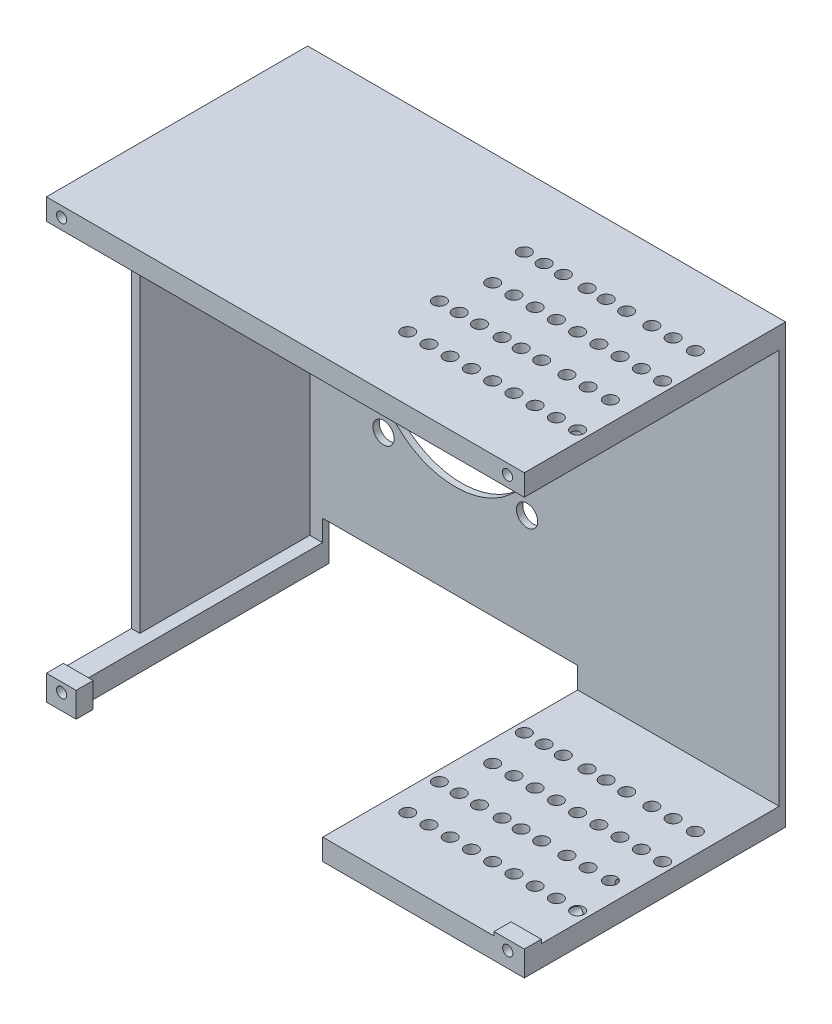
SolidWorks part; units mm, degrees
ref_plane "Front Plane" through (0, 0, 0) normal (0, 0, 1) x (1, 0, 0)
ref_plane "Top Plane" through (0, 0, 0) normal (0, 1, 0) x (1, 0, 0)
ref_plane "Right Plane" through (0, 0, 0) normal (1, 0, 0) x (0, 0, -1)
sketch "Sketch1" plane through (0, 0, 0) normal (0, 0, 1) x (1, 0, 0)
  line L1 (0, 0) -> (112.5, 0)
  line L2 (0, 0) -> (0, 103)
  line L3 (0, 103) -> (112.5, 103)
  line L4 (112.5, 0) -> (112.5, 103)
extrude "Boss-Extrude1" add sketch "Sketch1" along normal blind 1.5
sketch "Sketch2" plane through (0, 0, 1.5) normal (0, 0, 1) x (1, 0, 0)
  line L0 (112.5, 0) -> (112.5, 103) construction
  line L1 (0, 103) -> (112.5, 103)
  line L2 (0, 103) -> (0, 98)
  line L3 (0, 98) -> (112.5, 98)
  line L4 (112.5, 103) -> (112.5, 98)
extrude "Boss-Extrude2" add sketch "Sketch2" along normal blind 60
sketch "Sketch3" plane through (0, 0, 0) normal (0, 0, -1) x (-1, 0, 0)
  circle A0 centre (-36.25, 51.5) radius 19.5
  circle A1 centre (-53.1443, 68.3943) radius 2.5
  circle A2 centre (-19.3557, 68.3943) radius 2.5
  circle A3 centre (-19.3557, 34.6057) radius 2.5
  circle A4 centre (-53.1443, 34.6057) radius 2.5
  point P4 (-112.5, 103)
  point P18 (-36.25, 51.5)
  point P19 (-36.25, 51.5)
  point P25 (0, 0)
extrude "Cut-Extrude1" cut sketch "Sketch3" against normal blind 60
sketch "Sketch4" plane through (0, 0, 1.5) normal (0, 0, 1) x (1, 0, 0)
  line L0 (112.5, 0) -> (112.5, 98) construction
  line L1 (0, 0) -> (112.5, 0)
  line L2 (0, 0) -> (0, 5)
  line L3 (0, 5) -> (112.5, 5)
  line L4 (112.5, 0) -> (112.5, 5)
extrude "Boss-Extrude3" add sketch "Sketch4" along normal up to surface (60 mm away) up to face at (56.25, 100.5, 61.5)
sketch "Sketch5" plane through (0, 0, 1.5) normal (0, 0, 1) x (1, 0, 0)
  line L0 (112.5, 5) -> (0, 5) construction
  line L1 (0, 98) -> (2, 98)
  line L2 (0, 98) -> (0, 5)
  line L3 (0, 5) -> (2, 5)
  line L4 (2, 98) -> (2, 5)
extrude "Boss-Extrude4" add sketch "Sketch5" along normal blind 40
sketch "Sketch6" plane through (0, 0, 0) normal (0, 0, -1) x (-1, 0, 0)
  line L5 (0, 0) -> (-112.5, 0) construction
  line L7 (-5, 0) -> (-65.0477, 0)
  line L8 (-5, 0) -> (-5, 10)
  line L9 (-5, 10) -> (-65.0477, 10)
  line L10 (-65.0477, 0) -> (-65.0477, 10)
extrude "Cut-Extrude2" cut sketch "Sketch6" against normal blind 70
sketch "Sketch8" plane through (0, 0, 0) normal (0, -1, 0) x (1, 0, 0)
  circle A0 centre (110.0477, 46.5) radius 1.5
  circle A1 centre (105.0477, 46.5) radius 1.5
  circle A2 centre (100.0477, 46.5) radius 1.5
  circle A3 centre (95.0477, 46.5) radius 1.5
  circle A4 centre (90.0477, 46.5) radius 1.5
  circle A5 centre (85.0477, 46.5) radius 1.5
  circle A6 centre (80.0477, 46.5) radius 1.5
  circle A7 centre (75.0477, 46.5) radius 1.5
  circle A8 centre (70.0477, 46.5) radius 1.5
  circle A9 centre (107.7607, 36.5) radius 1.5
  circle A10 centre (102.5264, 36.5) radius 1.5
  circle A11 centre (97.5246, 36.5) radius 1.5
  circle A12 centre (91.5923, 36.5) radius 1.5
  circle A13 centre (86.7651, 36.5) radius 1.5
  circle A14 centre (82.2868, 36.5) radius 1.5
  circle A15 centre (76.9361, 36.5) radius 1.5
  circle A16 centre (72.167, 36.5) radius 1.5
  circle A17 centre (67.5, 36.5) radius 1.5
  circle A18 centre (110.0477, 26.5) radius 1.5
  circle A19 centre (105.0477, 26.5) radius 1.5
  circle A20 centre (100.0477, 26.5) radius 1.5
  circle A21 centre (95.0477, 26.5) radius 1.5
  circle A22 centre (90.0477, 26.5) radius 1.5
  circle A23 centre (85.0477, 26.5) radius 1.5
  circle A24 centre (80.0477, 26.5) radius 1.5
  circle A25 centre (75.0477, 26.5) radius 1.5
  circle A26 centre (70.0477, 26.5) radius 1.5
  circle A27 centre (107.7607, 16.5) radius 1.5
  circle A28 centre (102.5264, 16.5) radius 1.5
  circle A29 centre (97.5246, 16.5) radius 1.5
  circle A30 centre (91.5923, 16.5) radius 1.5
  circle A31 centre (86.7651, 16.5) radius 1.5
  circle A32 centre (82.2868, 16.5) radius 1.5
  circle A33 centre (76.6825, 16.5) radius 1.5
  circle A34 centre (72.167, 16.5) radius 1.5
  circle A35 centre (67.5, 16.5) radius 1.5
extrude "Cut-Extrude4" cut sketch "Sketch8" against normal up to surface (103 mm away) up to face at (56.25, 103, 30.75)
sketch "Sketch9" plane through (0, 0, 61.5) normal (0, 0, 1) x (1, 0, 0)
  line L1 (0, 5) -> (7, 5)
  line L2 (0, 5) -> (0, 0)
  line L3 (0, 0) -> (7, 0)
  line L4 (7, 5) -> (7, 0)
extrude "Boss-Extrude5" add sketch "Sketch9" against normal blind 3
sketch "Sketch12" plane through (0, 0, 0) normal (0, 0, -1) x (-1, 0, 0)
  circle A0 centre (-3.5789, 3.7602) radius 1.2
  circle A1 centre (-108.5991, 3.6351) radius 1.2
  circle A2 centre (-108.5454, 100.6013) radius 1.2
  circle A3 centre (-3.5789, 100.6013) radius 1.2
extrude "Cut-Extrude5" cut sketch "Sketch12" along normal blind 30 from surface
sketch "Sketch13" plane through (0, 0, 61.5) normal (0, 0, 1) x (1, 0, 0)
  line L1 (112.5, 0) -> (105.374, 0)
  line L2 (112.5, 0) -> (112.5, 5.8995)
  line L3 (112.5, 5.8995) -> (105.374, 5.8995)
  line L4 (105.374, 0) -> (105.374, 5.8995)
  line L5 (0, 0) -> (7.0019, 0)
  line L6 (0, 0) -> (0, 5.8995)
  line L7 (0, 5.8995) -> (7.0019, 5.8995)
  line L8 (7.0019, 0) -> (7.0019, 5.8995)
  circle A0 centre (108.5991, 3.6351) radius 1.2
  circle A1 centre (3.5789, 3.7602) radius 1.2
extrude "Boss-Extrude7" add sketch "Sketch13" against normal blind 4
